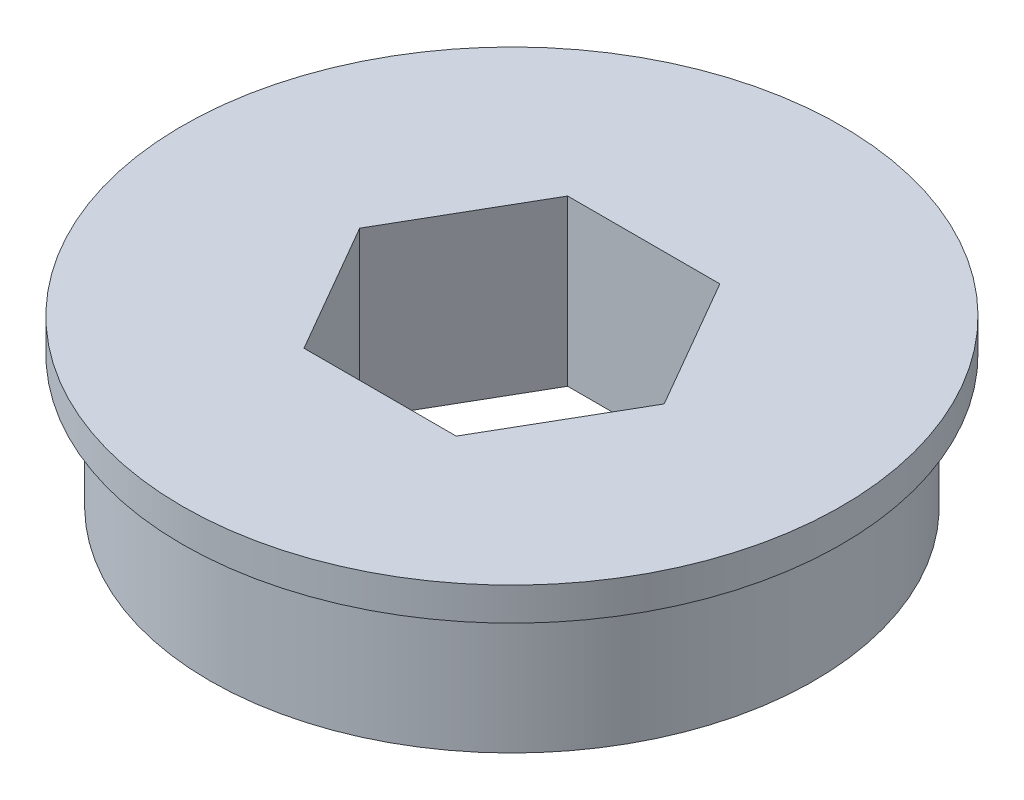
SolidWorks part; units mm, degrees
material "Plain Carbon Steel"
ref_plane "Front Plane" through (0, 0, 0) normal (0, 0, 1) x (1, 0, 0)
ref_plane "Top Plane" through (0, 0, 0) normal (0, 1, 0) x (1, 0, 0)
ref_plane "Right Plane" through (0, 0, 0) normal (1, 0, 0) x (0, 0, -1)
sketch "Sketch1" plane through (0, 0, 0) normal (0, 1, 0) x (1, 0, 0)
  line L1 (3.6662, 6.35) -> (-3.6662, 6.35)
  line L2 (-3.6662, 6.35) -> (-7.3323, 0)
  line L3 (-7.3323, 0) -> (-3.6662, -6.35)
  line L4 (-3.6662, -6.35) -> (3.6662, -6.35)
  line L5 (3.6662, -6.35) -> (7.3323, 0)
  line L6 (7.3323, 0) -> (3.6662, 6.35)
  circle A0 centre (0, 0) radius 14.5542
  circle A1 centre (0, 0) radius 6.35 construction
  dimension "D1" = 29.1084
  dimension "D2" = 12.7
extrude "Boss-Extrude1" add sketch "Sketch1" along normal blind 6.35
sketch "Sketch2" plane through (0, 6.35, 0) normal (0, 1, 0) x (1, 0, 0)
  line L0 (-3.6662, 6.35) -> (-7.3323, 0) construction
  line L1 (-7.3323, 0) -> (-3.6662, -6.35) construction
  line L2 (-3.6662, -6.35) -> (3.6662, -6.35) construction
  line L3 (3.6662, -6.35) -> (7.3323, 0) construction
  line L4 (7.3323, 0) -> (3.6662, 6.35) construction
  line L5 (3.6662, 6.35) -> (-3.6662, 6.35) construction
  line L6 (3.6662, 6.35) -> (-3.6662, 6.35)
  line L7 (7.3323, 0) -> (3.6662, 6.35)
  line L8 (3.6662, -6.35) -> (7.3323, 0)
  line L9 (-3.6662, -6.35) -> (3.6662, -6.35)
  line L10 (-7.3323, 0) -> (-3.6662, -6.35)
  line L11 (-3.6662, 6.35) -> (-7.3323, 0)
  circle A0 centre (0, 0) radius 15.875
  dimension "D1" = 31.75
extrude "Boss-Extrude2" add sketch "Sketch2" along normal blind 1.5875
